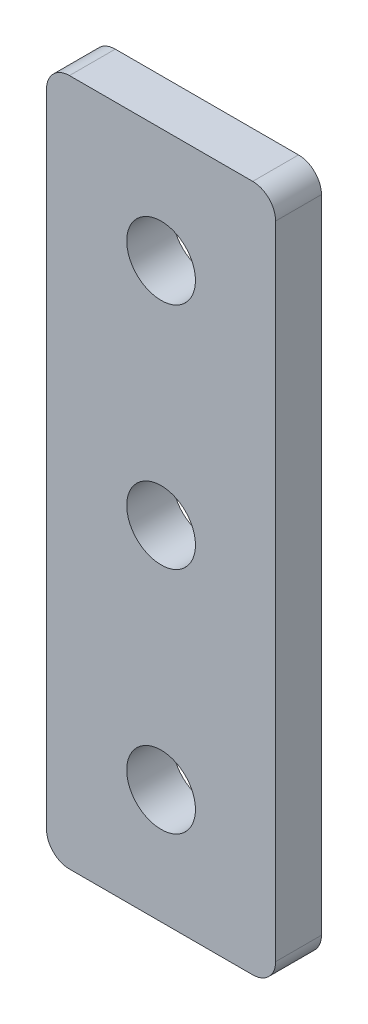
SolidWorks part; units mm, degrees
material "ABS"
ref_plane "前视基准面" through (0, 0, 0) normal (0, 0, 1) x (1, 0, 0)
ref_plane "上视基准面" through (0, 0, 0) normal (0, 1, 0) x (1, 0, 0)
ref_plane "右视基准面" through (0, 0, 0) normal (1, 0, 0) x (0, 0, -1)
other "Configuration Table"
sketch "草图1" plane through (0, 0, 0) normal (0, 0, 1) x (1, 0, 0)
  line L0 (1.6421, -1.909) -> (1.6421, -31.909) construction
  line L1 (-3.3579, -1.909) -> (6.6421, -1.909)
  line L2 (-3.3579, -1.909) -> (-3.3579, -31.909)
  line L3 (-3.3579, -31.909) -> (6.6421, -31.909)
  line L4 (6.6421, -1.909) -> (6.6421, -31.909)
  line L5 (-3.3579, -1.909) -> (6.6421, -31.909) construction
  line L6 (-3.3579, -31.909) -> (6.6421, -1.909) construction
  line L7 (-3.3579, -16.909) -> (6.6421, -16.909) construction
  circle A0 centre (1.6421, -6.909) radius 1.5
  circle A1 centre (1.6421, -16.909) radius 1.5
  circle A2 centre (1.6421, -26.909) radius 1.5
  point P4 (1.6421, -16.909)
  dimension "D3" = 3
  dimension "D4" = 10
  dimension "D1" = 10
  dimension "D2" = 30
extrude "凸台-拉伸1" add sketch "草图1" along normal blind 2
fillet "圆角1" radius 1 4 edges at (-3.3579, -31.909, 1) (6.6421, -31.909, 1) (-3.3579, -1.909, 1) (6.6421, -1.909, 1)
